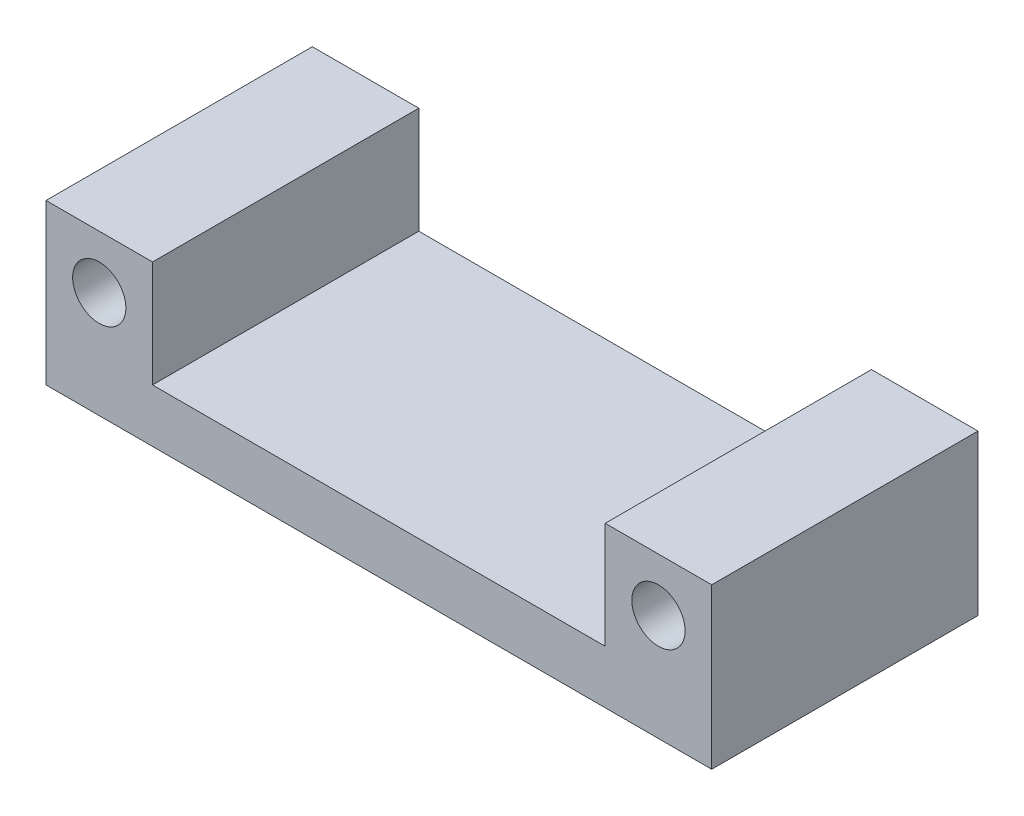
SolidWorks part; units mm, degrees
ref_plane "Front Plane" through (0, 0, 0) normal (0, 0, 1) x (1, 0, 0)
ref_plane "Top Plane" through (0, 0, 0) normal (0, 1, 0) x (1, 0, 0)
ref_plane "Right Plane" through (0, 0, 0) normal (1, 0, 0) x (0, 0, -1)
sketch "Sketch1" plane through (0, 0, 0) normal (0, 0, 1) x (1, 0, 0)
  line L0 (-125, 0) -> (125, 0)
  line L1 (125, 0) -> (125, 60)
  line L2 (125, 60) -> (85, 60)
  line L3 (85, 60) -> (85, 20)
  line L4 (85, 20) -> (-85, 20)
  line L5 (-85, 20) -> (-85, 60)
  line L6 (-85, 60) -> (-125, 60)
  line L7 (-125, 60) -> (-125, 0)
  circle A0 centre (-105, 40) radius 10
  circle A1 centre (105, 40) radius 10
  point P8 (0, 0)
  point P14 (0, 0)
  point P15 (0, 0)
  point P16 (105, 60)
  point P17 (-105, 60)
  dimension "D1" = 40
  dimension "D2" = 40
  dimension "D3" = 250
extrude "Boss-Extrude1" add sketch "Sketch1" along normal blind 100 contours L6 L7 L0 L1 L2 L3 L4 L5
sketch "Sketch2" plane through (0, 0, 100) normal (0, 0, 1) x (1, 0, 0)
  line L0 (-85, 60) -> (-125, 60) construction
  line L1 (125, 60) -> (85, 60) construction
  circle A0 centre (-105, 40) radius 10
  circle A1 centre (105, 40) radius 10
  point P4 (0, 0)
  point P7 (-105, 60)
  point P8 (0, 0)
  point P11 (105, 60)
extrude "Cut-Extrude1" cut sketch "Sketch2" against normal blind 130
